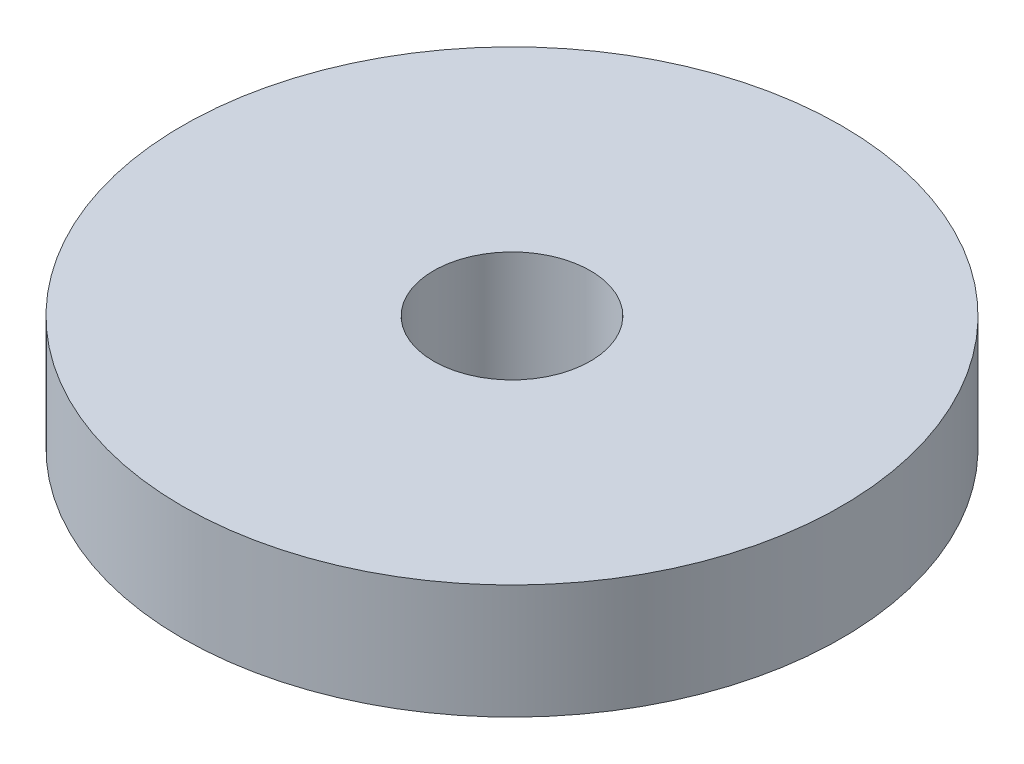
SolidWorks part; units mm, degrees
material "AISI 1020"
ref_plane "Front Plane" through (0, 0, 0) normal (0, 0, 1) x (1, 0, 0)
ref_plane "Top Plane" through (0, 0, 0) normal (0, 1, 0) x (1, 0, 0)
ref_plane "Right Plane" through (0, 0, 0) normal (1, 0, 0) x (0, 0, -1)
sketch "Sketch1" plane through (0, 0, 0) normal (0, 1, 0) x (1, 0, 0)
  circle A0 centre (0, 0) radius 3.2639
  circle A1 centre (0, 0) radius 13.716
  dimension "D1" = 27.432
  dimension "D2" = 6.5278
extrude "Boss-Extrude1" add sketch "Sketch1" along normal blind 4.7625
equation "\"OD\"= 1.08"
equation "\"ID\"= 0.257"
equation "\"thk\"= 0.1875"
equation "\"D1@Sketch1\"=\"OD\""
equation "\"D2@Sketch1\"=\"ID\""
equation "\"D1@Boss-Extrude1\"=\"thk\""
